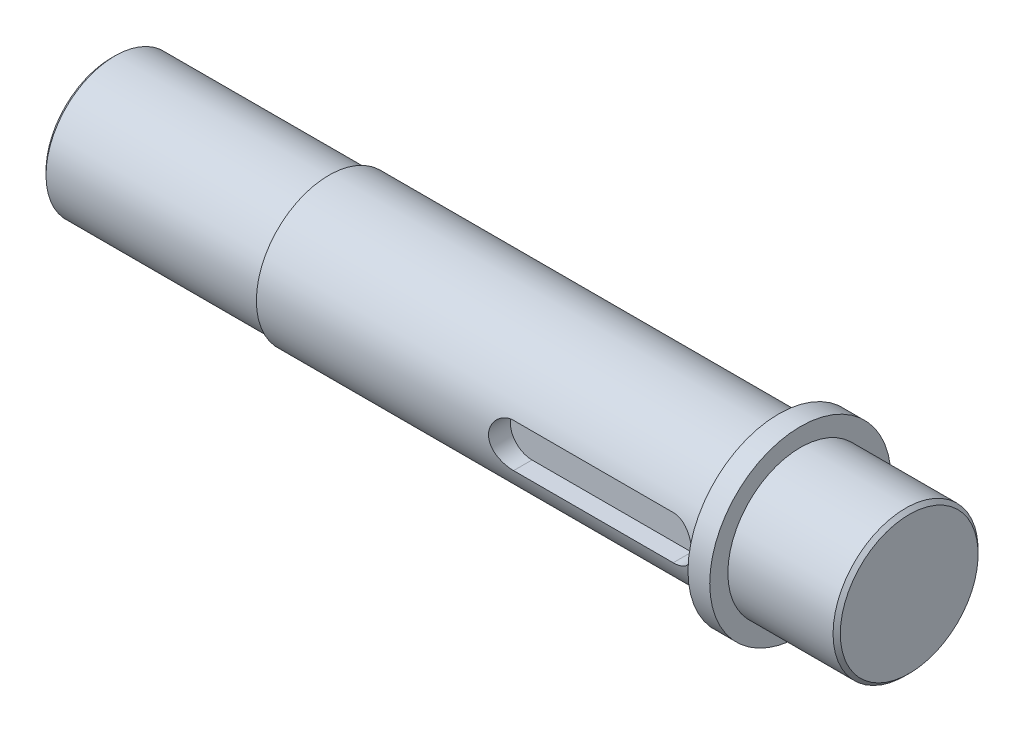
SolidWorks part; units mm, degrees
ref_plane "前视基准面" through (0, 0, 0) normal (0, 0, 1) x (1, 0, 0)
ref_plane "上视基准面" through (0, 0, 0) normal (0, 1, 0) x (1, 0, 0)
ref_plane "右视基准面" through (0, 0, 0) normal (1, 0, 0) x (0, 0, -1)
sketch "草图1" plane through (0, 0, 0) normal (0, 0, 1) x (1, 0, 0)
  line L0 (-40.4651, 0) -> (56.6512, 0) construction
  line L1 (0, 0) -> (0, 9.5)
  line L2 (0, 9.5) -> (30, 9.5)
  line L3 (30, 9.5) -> (30, 10)
  line L4 (30, 10) -> (92, 10)
  line L5 (92, 10) -> (92, 12.5)
  line L6 (92, 12.5) -> (95, 12.5)
  line L7 (95, 12.5) -> (95, 10)
  line L8 (95, 10) -> (110, 10)
  line L9 (110, 10) -> (110, 0)
  line L10 (110, 0) -> (0, 0)
  dimension "D1" = 9.5
  dimension "D2" = 10
  dimension "D3" = 12.5
  dimension "D4" = 110
  dimension "D5" = 30
  dimension "D6" = 62
  dimension "D7" = 3
revolve "旋转1" add sketch "草图1" angle 360 about L0
ref_plane "基准面1" through (0, 0, 10) normal (0, 0, 1) x (1, 0, 0)
sketch "草图3" plane through (0, 0, 10) normal (0, 0, 1) x (1, 0, 0)
  line L0 (65, 0) -> (87, 0) construction
  line L1 (65, 3) -> (87, 3)
  line L2 (65, -3) -> (87, -3)
  line L3 (92, 10) -> (92, -10) construction
  arc A0 (65, 3) -> (65, -3) centre (65, 0) ccw
  arc A1 (87, -3) -> (87, 3) centre (87, 0) ccw
  point P3 (76, 0)
  point P8 (90, 0)
  point P9 (62, 0)
  dimension "D1" = 28
  dimension "D2" = 6
  dimension "D3" = 5
extrude "切除-拉伸1" cut sketch "草图3" against normal blind 3
chamfer "倒角1" distance 0.5 angle 45 1 edges at (0, 0, 9.5)
chamfer "倒角2" distance 0.5 angle 45 1 edges at (110, 0, 10)
